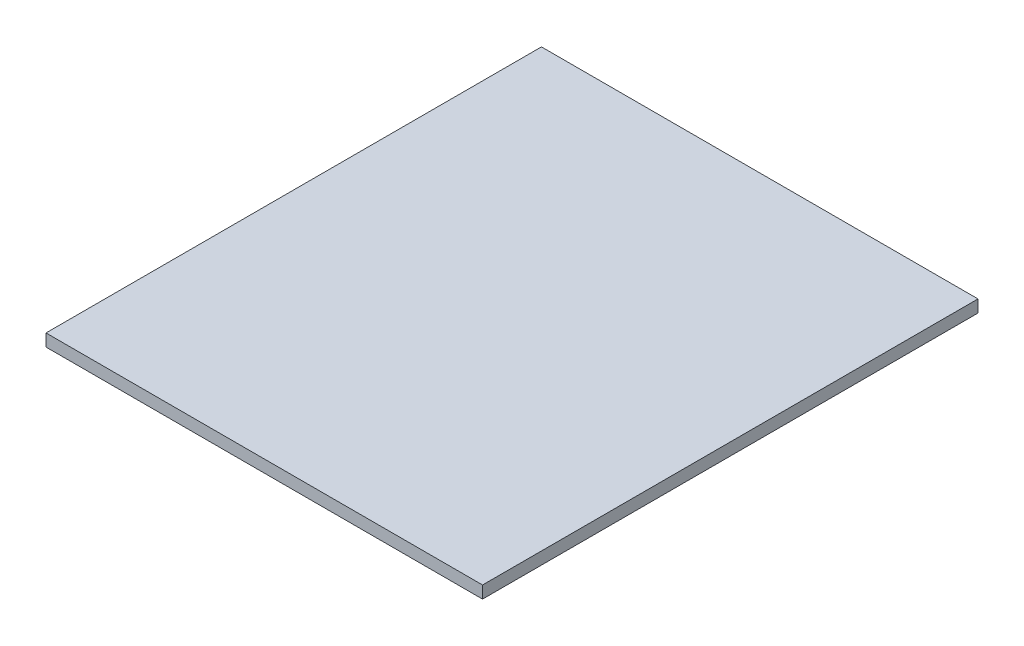
SolidWorks part; units mm, degrees
material "Polyurethane Foam Flexible"
ref_plane "Front Plane" through (0, 0, 0) normal (0, 0, 1) x (1, 0, 0)
ref_plane "Top Plane" through (0, 0, 0) normal (0, 1, 0) x (1, 0, 0)
ref_plane "Right Plane" through (0, 0, 0) normal (1, 0, 0) x (0, 0, -1)
sketch "Sketch1" plane through (0, 0, 0) normal (0, 1, 0) x (1, 0, 0)
  line L1 (-1130.173, 1282.7) -> (1130.173, 1282.7)
  line L2 (-1130.173, 1282.7) -> (-1130.173, -1282.7)
  line L3 (-1130.173, -1282.7) -> (1130.173, -1282.7)
  line L4 (1130.173, 1282.7) -> (1130.173, -1282.7)
  line L5 (-1130.173, 1282.7) -> (1130.173, -1282.7) construction
  line L6 (-1130.173, -1282.7) -> (1130.173, 1282.7) construction
  point P0 (0, 0)
  dimension "D1" = 2260.346
  dimension "D2" = 2565.4
extrude "Boss-Extrude1" add sketch "Sketch1" along normal blind 63.5
